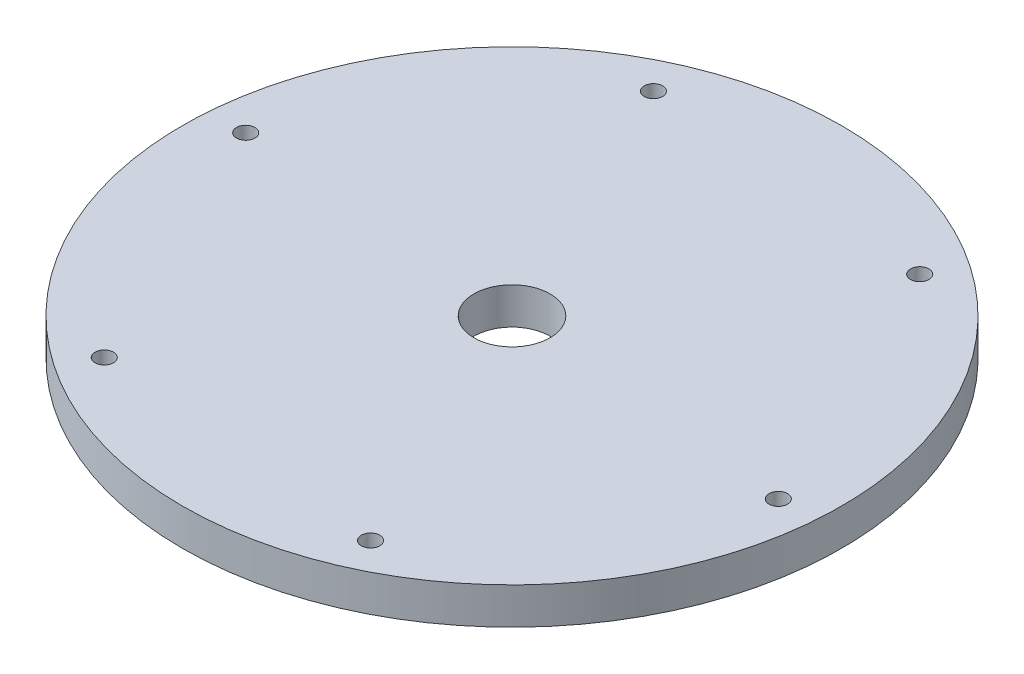
SolidWorks part; units mm, degrees
ref_plane "Front Plane" through (0, 0, 0) normal (0, 0, 1) x (1, 0, 0)
ref_plane "Top Plane" through (0, 0, 0) normal (0, 1, 0) x (1, 0, 0)
ref_plane "Right Plane" through (0, 0, 0) normal (1, 0, 0) x (0, 0, -1)
sketch "Sketch1" plane through (0, 0, 0) normal (0, 1, 0) x (1, 0, 0)
  circle A0 centre (0, 0) radius 53.5432
  circle A1 centre (0, 0) radius 6.1849
  circle A2 centre (47.3896, -4.1253) radius 1.4986
  circle A3 centre (0, 0) radius 47.5689 construction
  circle A4 centre (20.1222, -43.1033) radius 1.4986
  circle A5 centre (0, 0) radius 47.5689 construction
  circle A6 centre (-27.2675, -38.978) radius 1.4986
  circle A7 centre (0, 0) radius 47.5689 construction
  circle A8 centre (-47.3896, 4.1253) radius 1.4986
  circle A9 centre (0, 0) radius 47.5689 construction
  circle A10 centre (-20.1222, 43.1033) radius 1.4986
  circle A11 centre (0, 0) radius 47.5689 construction
  circle A12 centre (27.2675, 38.978) radius 1.4986
  circle A13 centre (0, 0) radius 47.5689 construction
  point P7 (45.891, -4.1253)
  point P8 (53.384, -4.1253)
  point P32 (0, 0)
  dimension "D1" = 107.0864
  dimension "D2" = 12.3698
  dimension "D3" = 2.9972
  dimension "D4" = 7.493
  dimension "D5" = 6
extrude "Boss-Extrude1" add sketch "Sketch1" along normal blind 5.9563
